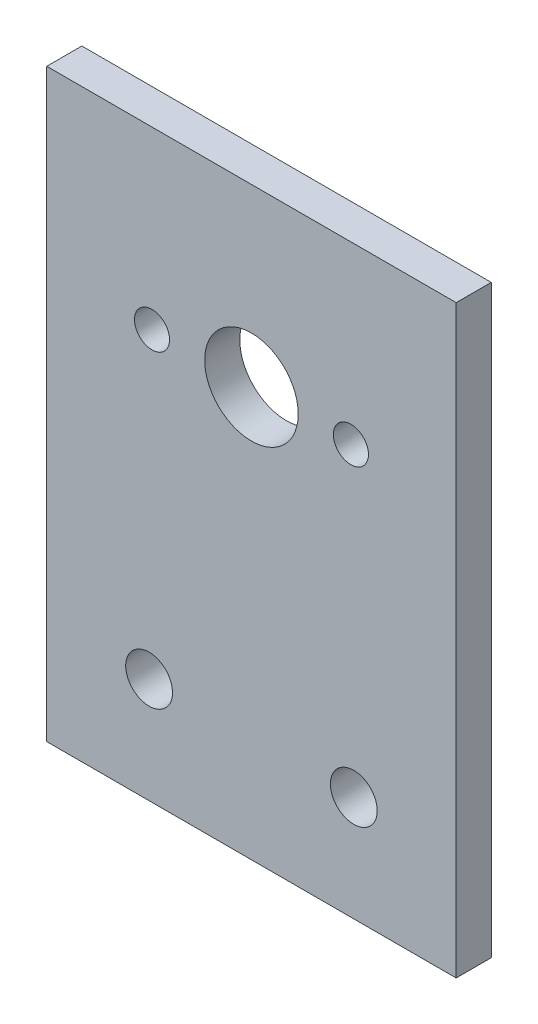
SolidWorks part; units mm, degrees
ref_plane "Front Plane" through (0, 0, 0) normal (0, 0, 1) x (1, 0, 0)
ref_plane "Top Plane" through (0, 0, 0) normal (0, 1, 0) x (1, 0, 0)
ref_plane "Right Plane" through (0, 0, 0) normal (1, 0, 0) x (0, 0, -1)
sketch "Sketch1" plane through (0, 0, 0) normal (0, 0, 1) x (1, 0, 0)
  line L1 (-17.5, 25) -> (17.5, 25)
  line L2 (-17.5, 25) -> (-17.5, -25)
  line L3 (-17.5, -25) -> (17.5, -25)
  line L4 (17.5, 25) -> (17.5, -25)
  line L5 (-17.5, 25) -> (17.5, -25) construction
  line L6 (-17.5, -25) -> (17.5, 25) construction
  circle A0 centre (8.75, -16) radius 2
  circle A1 centre (-8.75, -16) radius 2
  circle A2 centre (0, 10) radius 4
  circle A3 centre (8.5, 10) radius 1.5
  circle A4 centre (-8.5, 10) radius 1.5
  point P0 (0, 0)
  dimension "D3" = 17
  dimension "D1" = 35
  dimension "D2" = 50
extrude "Boss-Extrude1" add sketch "Sketch1" along normal blind 3
